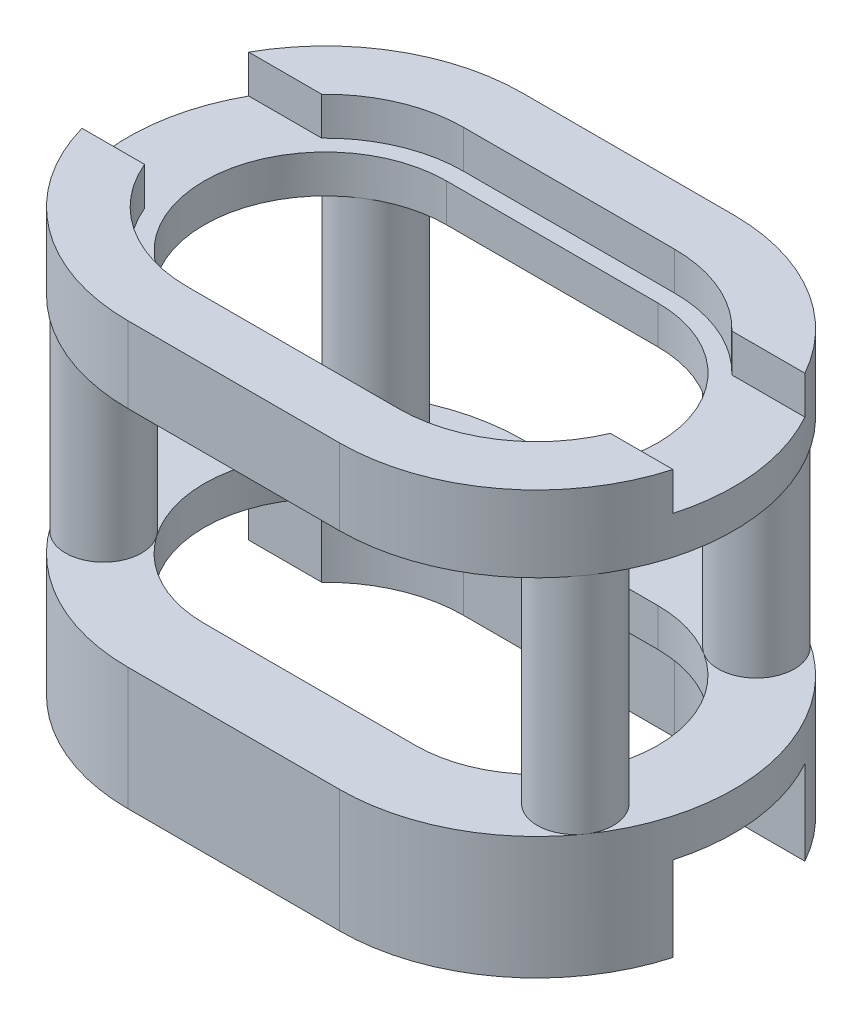
SolidWorks part; units mm, degrees
ref_plane "Front Plane" through (0, 0, 0) normal (0, 0, 1) x (1, 0, 0)
ref_plane "Top Plane" through (0, 0, 0) normal (0, 1, 0) x (1, 0, 0)
ref_plane "Right Plane" through (0, 0, 0) normal (1, 0, 0) x (0, 0, -1)
sketch "Sketch1" plane through (0, 0, 0) normal (0, 1, 0) x (1, 0, 0)
  line L0 (0, 0) -> (5, 0) construction
  line L1 (0, 3.2665) -> (5, 3.2665)
  line L2 (0, -3.2665) -> (5, -3.2665)
  line L3 (0, 4.6665) -> (5, 4.6665)
  line L4 (0, -4.6665) -> (5, -4.6665)
  arc A0 (0, 3.2665) -> (0, -3.2665) centre (0, 0) ccw
  arc A1 (5, -3.2665) -> (5, 3.2665) centre (5, 0) ccw
  arc A2 (5, -4.6665) -> (5, 4.6665) centre (5, 0) ccw
  arc A3 (0, 4.6665) -> (0, -4.6665) centre (0, 0) ccw
  point P3 (2.5, 0)
  dimension "D1" = 1.4
extrude "Boss-Extrude1" add sketch "Sketch1" along normal blind 10
ref_plane "Plane1" through (0, 2, 0) normal (0, 1, 0) x (1, 0, 0)
sketch "Sketch2" plane through (0, 2, 0) normal (0, 1, 0) x (1, 0, 0)
  line L0 (0, 0) -> (5, 0) construction
  line L1 (0, 2.8665) -> (5, 2.8665)
  line L2 (0, -2.8665) -> (5, -2.8665)
  line L3 (0, 3.2665) -> (5, 3.2665)
  line L4 (0, -3.2665) -> (5, -3.2665)
  arc A0 (0, 2.8665) -> (0, -2.8665) centre (0, 0) ccw
  arc A1 (5, -2.8665) -> (5, 2.8665) centre (5, 0) ccw
  arc A2 (5, -3.2665) -> (5, 3.2665) centre (5, 0) ccw
  arc A3 (0, 3.2665) -> (0, -3.2665) centre (0, 0) ccw
  point P3 (2.5, 0)
  dimension "D1" = 0.4
extrude "Boss-Extrude2" add sketch "Sketch2" along normal blind 7.1
sketch "Sketch3" plane through (0, 0, 4.6665) normal (0, 0, 1) x (1, 0, 0)
  line L0 (5.1332, 2) -> (-5.1332, 2) construction
  line L1 (-4.5123, 8.2) -> (9.5123, 8.2)
  line L2 (-4.5123, 8.2) -> (-4.5123, 2.9)
  line L3 (-4.5123, 2.9) -> (9.5123, 2.9)
  line L4 (9.5123, 8.2) -> (9.5123, 2.9)
  line L5 (-4.5123, 8.2) -> (9.5123, 2.9) construction
  line L6 (-4.5123, 2.9) -> (9.5123, 8.2) construction
  line L7 (9.6665, 10) -> (5, 10) construction
  point P0 (2.5, 5.55)
  point P9 (0, 0)
  point P10 (0, 0)
  point P11 (0, 0)
  point P12 (0, 0)
  point P13 (0, 0)
  dimension "D1" = 1.8
  dimension "D2" = 0.9
extrude "Cut-Extrude1" cut sketch "Sketch3" against normal blind 10
sketch "Sketch4" plane through (0, 10, 0) normal (0, 1, 0) x (1, 0, 0)
  line L0 (5, 3.2665) -> (0, 3.2665) construction
  line L1 (10, -1.2665) -> (-5, -1.2665)
  line L2 (10, -1.2665) -> (10, 2.2665)
  line L3 (10, 2.2665) -> (-5, 2.2665)
  line L4 (-5, -1.2665) -> (-5, 2.2665)
  line L5 (10, -1.2665) -> (-5, 2.2665) construction
  line L6 (10, 2.2665) -> (-5, -1.2665) construction
  line L7 (0, -3.2665) -> (5, -3.2665) construction
  point P0 (2.5, 0.5)
  dimension "D1" = 1
  dimension "D2" = 2
  dimension "D3" = 15
extrude "Cut-Extrude2" cut sketch "Sketch4" against normal blind 0.9
sketch "Sketch5" plane through (0, 0, 0) normal (0, -1, 0) x (1, 0, 0)
  line L2 (10, -2.2665) -> (-5, -2.2665)
  line L3 (10, -2.2665) -> (10, 1.2665)
  line L4 (10, 1.2665) -> (-5, 1.2665)
  line L5 (-5, -2.2665) -> (-5, 1.2665)
  line L6 (10, -2.2665) -> (-5, 1.2665) construction
  line L8 (10, 1.2665) -> (-5, -2.2665) construction
  point P0 (2.5, -0.5)
extrude "Cut-Extrude3" cut sketch "Sketch5" against normal blind 2
sketch "Sketch7" plane through (0, 2, 0) normal (0, 1, 0) x (1, 0, 0)
  circle A0 centre (-2.0017, 3.1905) radius 0.9
  circle A1 centre (7.0166, 3.1812) radius 0.9
  circle A2 centre (-3.081, -2.1665) radius 0.9
  circle A3 centre (8.081, -2.1665) radius 0.9
extrude "Boss-Extrude3" add sketch "Sketch7" along normal blind 7.1
ref_plane "Plane2" through (10, 0, 0) normal (1, 0, 0) x (0, 0, -1)
sketch "Sketch8" plane through (10, 0, 0) normal (1, 0, 0) x (0, 0, -1)
  line L2 (-1.1897, 8.2) -> (1.1897, 8.2)
  line L3 (-1.1897, 8.2) -> (-1.1897, 2.9)
  line L4 (-1.1897, 2.9) -> (1.1897, 2.9)
  line L5 (1.1897, 8.2) -> (1.1897, 2.9)
extrude "Cut-Extrude4" cut sketch "Sketch8" against normal blind 15
